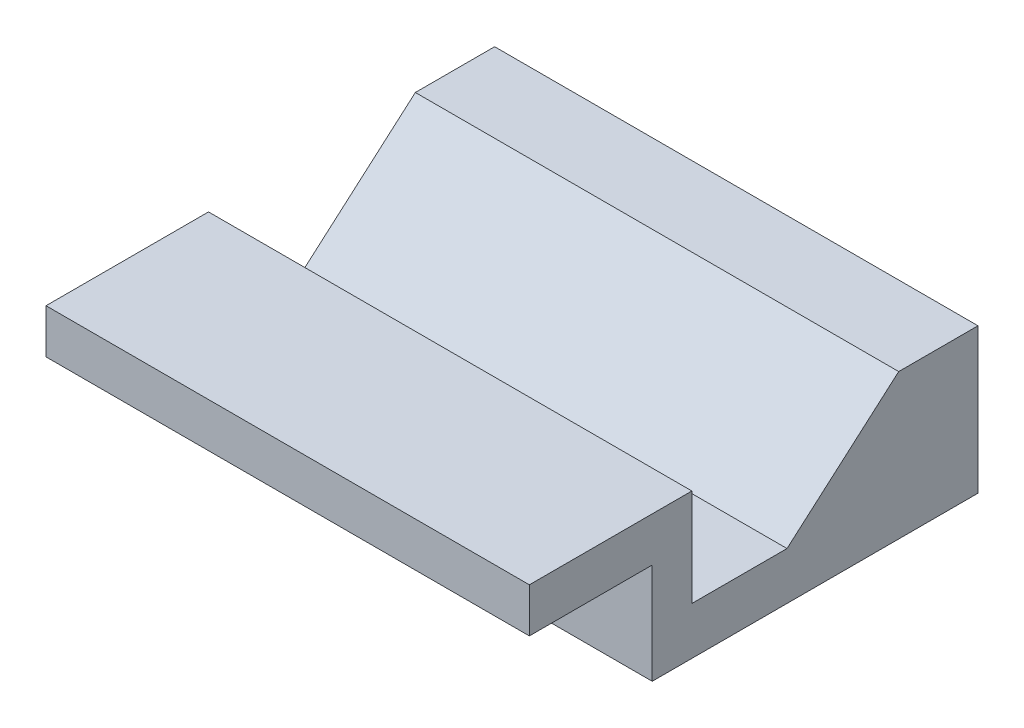
SolidWorks part; units mm, degrees
ref_plane "Front Plane" through (0, 0, 0) normal (0, 0, 1) x (1, 0, 0)
ref_plane "Top Plane" through (0, 0, 0) normal (0, 1, 0) x (1, 0, 0)
ref_plane "Right Plane" through (0, 0, 0) normal (1, 0, 0) x (0, 0, -1)
sketch "Sketch1" plane through (0, 0, 0) normal (1, 0, 0) x (0, 0, -1)
  line L0 (0, 0) -> (0, -2.794)
  line L1 (0, -2.794) -> (7.747, -2.794)
  line L2 (7.747, -2.794) -> (7.747, -9.144)
  line L3 (7.747, -9.144) -> (28.29, -9.144)
  line L4 (28.29, -9.144) -> (28.29, 0)
  line L5 (28.29, 0) -> (23.29, 0)
  line L6 (23.29, 0) -> (16.247, -6.144)
  line L7 (16.247, -6.144) -> (10.247, -6.144)
  line L8 (10.247, -6.144) -> (10.247, 0)
  line L9 (10.247, 0) -> (0, 0)
  line L10 (28.29, -9.144) -> (34.29, -9.144)
  line L11 (34.29, -9.144) -> (34.29, -21.59)
  line L12 (34.29, -21.59) -> (35.814, -23.114)
  line L13 (35.814, -22.114) -> (35.814, -23.114)
  line L14 (35.814, -22.114) -> (35.29, -21.59)
  line L15 (35.29, -21.59) -> (35.29, -8.144)
  line L16 (35.29, -8.144) -> (28.29, -8.144)
  line L17 (34.29, -21.59) -> (35.29, -21.59) construction
  dimension "D1" = 7.747
  dimension "D2" = 2.794
  dimension "D3" = 23.114
  dimension "D4" = 45
  dimension "D5" = 13.97
  dimension "D6" = 1.524
  dimension "D7" = 1
  dimension "D8" = 1
  dimension "D9" = 35.814
  dimension "D10" = 2.5
  dimension "D11" = 3
  dimension "D12" = 7
  dimension "D13" = 6
  dimension "D14" = 5
extrude "Boss-Extrude1" add sketch "Sketch1" along normal blind 30.48 contours L8 L9 L0 L1 L2 L3 L4 L5 L6 L7
sketch "Sketch2" plane through (0, 0, 0) normal (0, 1, 0) x (1, 0, 0)
  line L0 (9.8777, 28.29) -> (0, 10.247)
  line L1 (30.48, 28.29) -> (0, 28.29) construction
  line L2 (0, 10.247) -> (0, 0) construction
  line L3 (30.48, 10.247) -> (0, 10.247) construction
  line L4 (20.6023, 28.29) -> (30.48, 10.247)
  line L5 (30.48, 0) -> (0, 0) construction
  circle A0 centre (5.08, 3.937) radius 2.3495
  circle A1 centre (15.24, 3.937) radius 2.3495
  circle A2 centre (25.4, 3.937) radius 2.3495
  point P19 (0, 0)
  dimension "D5" = 4.699
  dimension "D1" = 5.08
  dimension "D2" = 10.16
  dimension "D3" = 10.16
  dimension "D4" = 3.937
equation "\"D8@Sketch1\"=\"D7@Sketch1\""
equation "\"D3@Sketch2\"=\"D2@Sketch2\""
